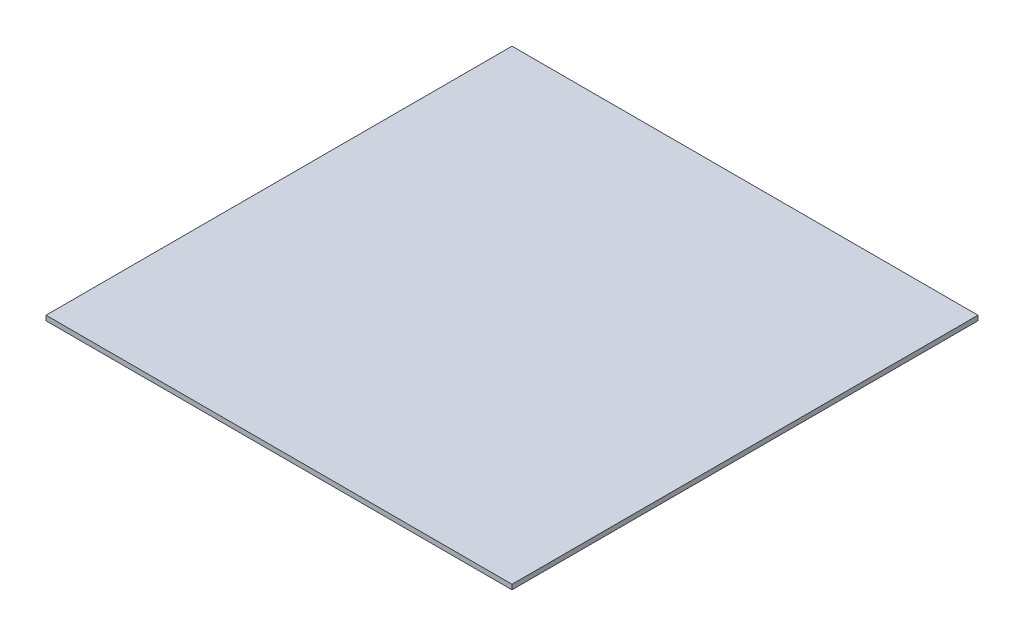
SolidWorks part; units mm, degrees
ref_plane "Front Plane" through (0, 0, 0) normal (0, 0, 1) x (1, 0, 0)
ref_plane "Top Plane" through (0, 0, 0) normal (0, 1, 0) x (1, 0, 0)
ref_plane "Right Plane" through (0, 0, 0) normal (1, 0, 0) x (0, 0, -1)
sketch "Sketch1" plane through (0, 0, 0) normal (0, 1, 0) x (1, 0, 0)
  line L0 (-304.8, 0) -> (304.8, 0) construction
  line L1 (-304.8, -304.8) -> (304.8, -304.8)
  line L2 (-304.8, -304.8) -> (-304.8, 304.8)
  line L3 (-304.8, 304.8) -> (304.8, 304.8)
  line L4 (304.8, -304.8) -> (304.8, 304.8)
  dimension "D1" = 609.6
  dimension "D2" = 609.6
extrude "Boss-Extrude1" add sketch "Sketch1" along normal blind 6.35
